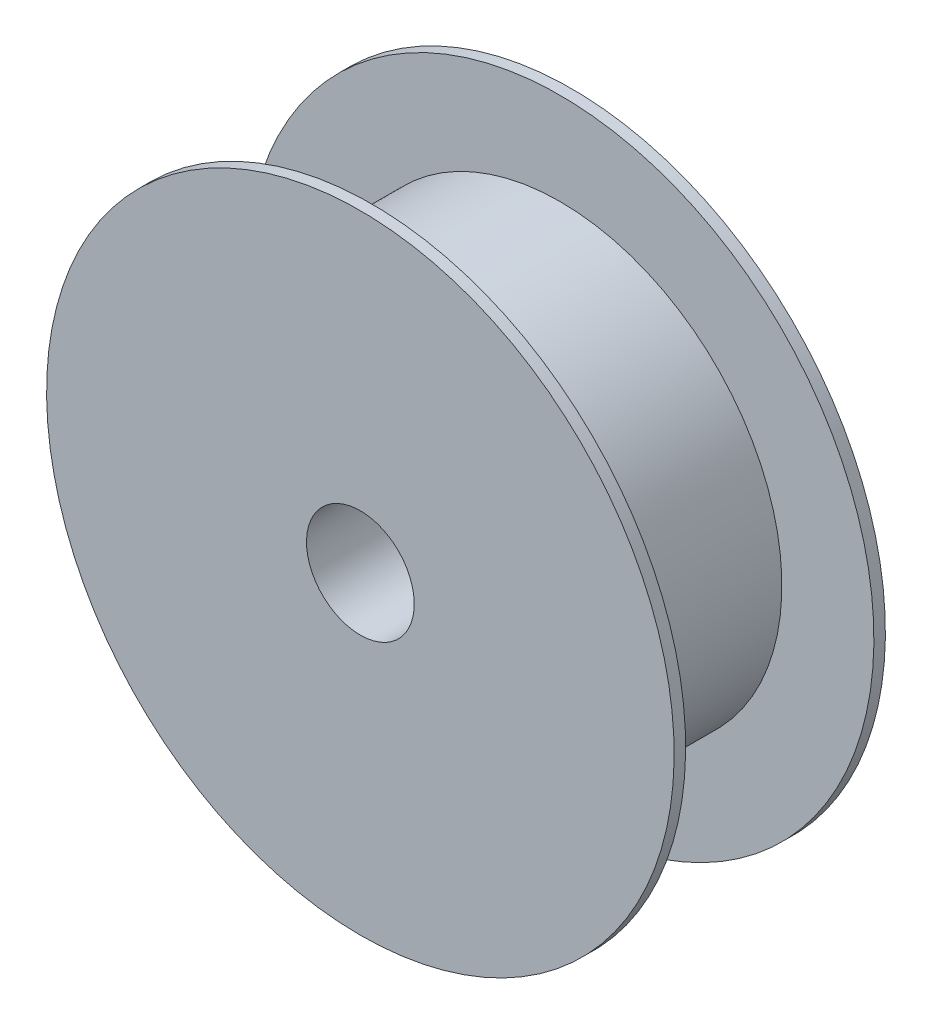
SolidWorks part; units mm, degrees
material "acero"
ref_plane "Alzado" through (0, 0, 0) normal (0, 0, 1) x (1, 0, 0)
ref_plane "Planta" through (0, 0, 0) normal (0, 1, 0) x (1, 0, 0)
ref_plane "Vista lateral" through (0, 0, 0) normal (1, 0, 0) x (0, 0, -1)
sketch "Croquis1" plane through (0, 0, 0) normal (1, 0, 0) x (0, 0, -1)
  line L0 (-50.5, 0) -> (50.5, 0)
  line L1 (-50.5, 150) -> (-50.5, 25.75)
  line L2 (50.5, 150) -> (50.5, 25.75)
  line L3 (-45, 150) -> (-45, 25.75)
  line L4 (45, 150) -> (45, 25.75)
  line L5 (-45, 0) -> (45, 0) construction
  line L6 (-50.5, 150) -> (-45, 150)
  line L7 (-50.5, -150) -> (-45, -150)
  line L8 (45, 150) -> (50.5, 150)
  line L9 (45, -150) -> (50.5, -150)
  line L10 (0, 106) -> (0, -106) construction
  line L11 (0, 25.75) -> (0, -25.75) construction
  line L12 (45, 106) -> (-45, 106)
  line L13 (50.5, -106) -> (-50.5, -106)
  line L14 (-50.5, 25.75) -> (50.5, 25.75)
  line L15 (-50.5, -25.75) -> (50.5, -25.75)
  line L16 (-50.5, -25.75) -> (-50.5, -150)
  line L17 (45, -25.75) -> (45, -150)
  line L18 (50.5, -25.75) -> (50.5, -150)
  line L19 (-45, -25.75) -> (-45, -150)
  point P6 (0, 0)
  point P15 (0, 0)
  point P23 (0, 0)
  point P24 (0, 0)
  dimension "D1" = 101
  dimension "D2" = 300
  dimension "D3" = 90
  dimension "D4" = 212
  dimension "D5" = 51.5
revolve "Revolución1" add sketch "Croquis1" angle 360 about L0
